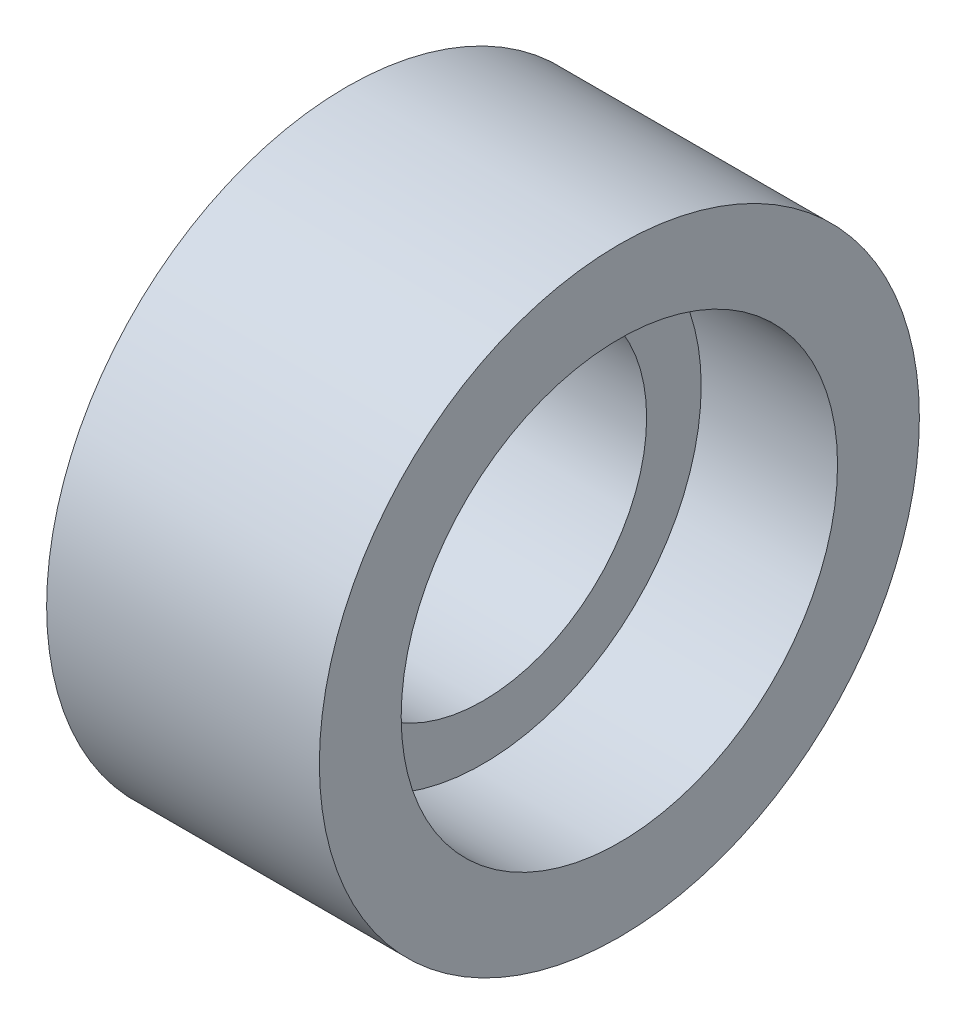
SolidWorks part; units mm, degrees
ref_plane "Plan de face" through (0, 0, 0) normal (0, 0, 1) x (1, 0, 0)
ref_plane "Plan de dessus" through (0, 0, 0) normal (0, 1, 0) x (1, 0, 0)
ref_plane "Plan de droite" through (0, 0, 0) normal (1, 0, 0) x (0, 0, -1)
sketch "Esquisse1" plane through (0, 0, 0) normal (0, 0, 1) x (1, 0, 0)
  line L0 (0, 0) -> (25.003, 0) construction
  line L1 (10.9259, 6) -> (10.9259, 11)
  line L2 (15.9259, 8) -> (15.9259, 6)
  line L3 (10.9259, 11) -> (20.9259, 11)
  line L4 (20.9259, 11) -> (20.9259, 8)
  line L5 (20.9259, 8) -> (15.9259, 8)
  line L6 (15.9259, 6) -> (10.9259, 6)
  dimension "D1" = 5
  dimension "D2" = 11
  dimension "D3" = 8
  dimension "D4" = 6
  dimension "D5" = 5
revolve "Révolution1" add sketch "Esquisse1" angle 360 about L0
